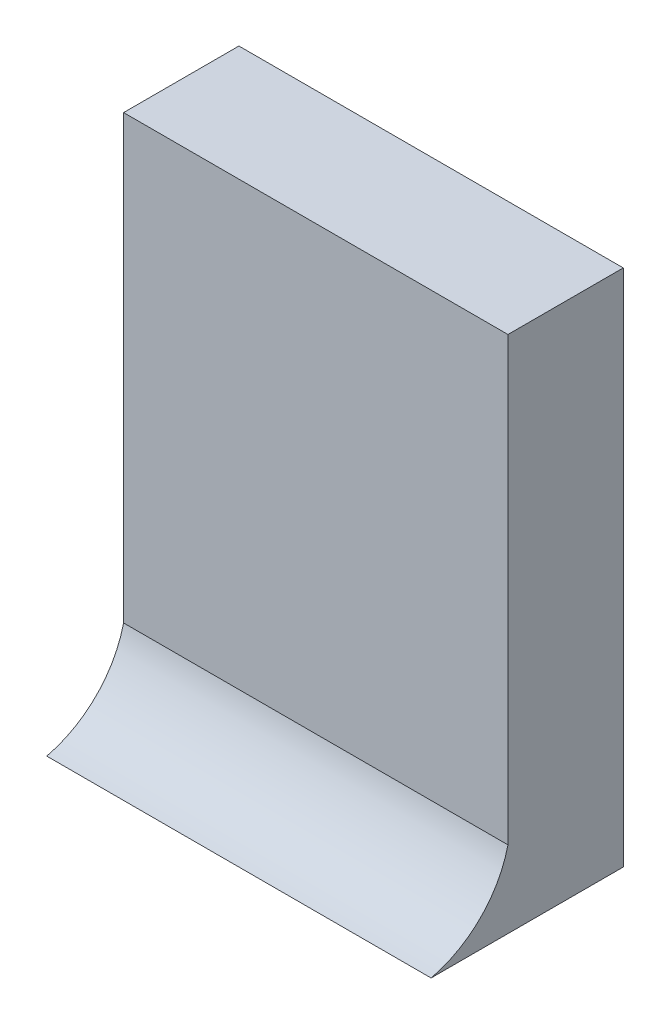
SolidWorks part; units mm, degrees
ref_plane "前视基准面" through (0, 0, 0) normal (0, 0, 1) x (1, 0, 0)
ref_plane "上视基准面" through (0, 0, 0) normal (0, 1, 0) x (1, 0, 0)
ref_plane "右视基准面" through (0, 0, 0) normal (1, 0, 0) x (0, 0, -1)
sketch "草图1" plane through (0, 0, 0) normal (0, 0, 1) x (1, 0, 0)
  line L1 (-25, 33.75) -> (25, 33.75)
  line L2 (-25, 33.75) -> (-25, -33.75)
  line L3 (-25, -33.75) -> (25, -33.75)
  line L4 (25, 33.75) -> (25, -33.75)
  line L5 (-25, 33.75) -> (25, -33.75) construction
  line L6 (-25, -33.75) -> (25, 33.75) construction
  point P0 (0, 0)
  dimension "D1" = 67.5
  dimension "D2" = 50
extrude "凸台-拉伸1" add sketch "草图1" along normal blind 15
sketch "草图5" plane through (25, 0, 0) normal (1, 0, 0) x (0, 0, -1)
  line L0 (-15, -33.75) -> (-25, -33.75)
  line L1 (-15, -33.75) -> (-15, -23.75)
  line L2 (-15, -33.75) -> (-15, 33.75) construction
  arc A0 (-15, -23.75) -> (-25, -33.75) centre (-28.0655, -20.6845) cw
  dimension "D3" = 13.4204
  dimension "D1" = 10
  dimension "D2" = 10
extrude "凸台-拉伸2" add sketch "草图5" against normal up to surface (50 mm away) up to face at (-25, 0, 7.5)
